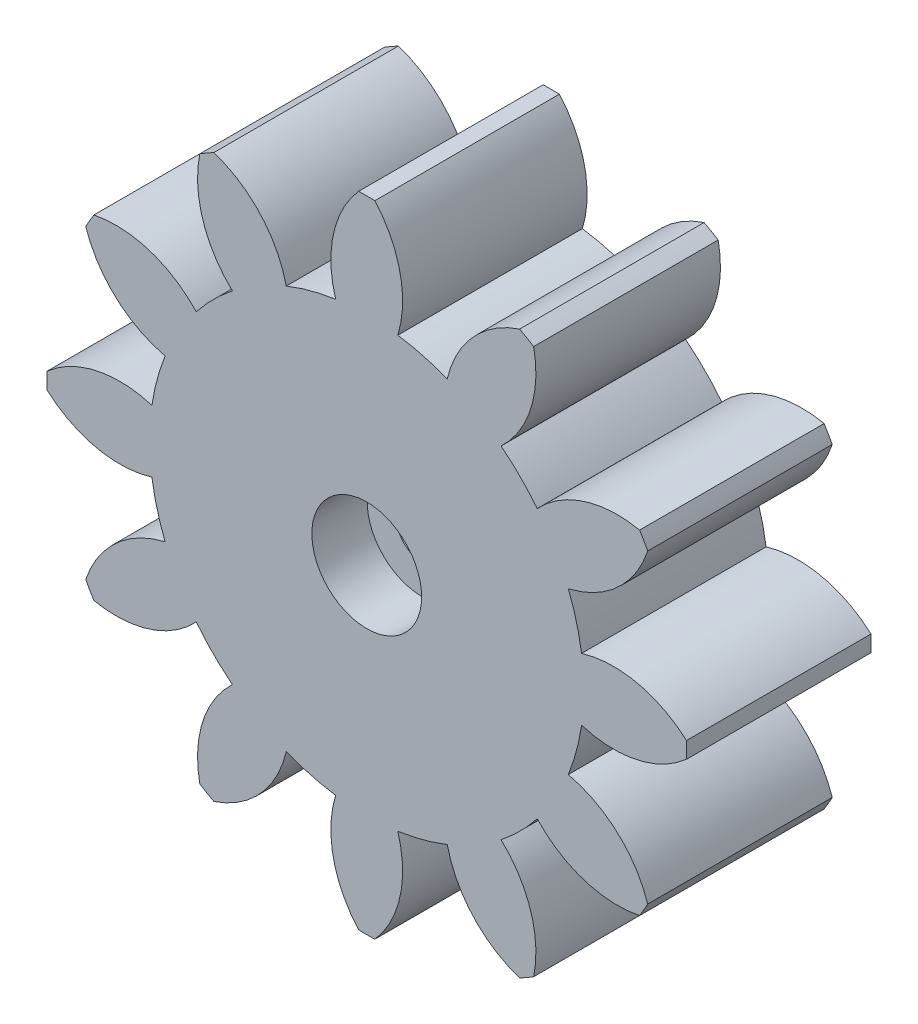
SolidWorks part; units mm, degrees
ref_plane "Front Plane" through (0, 0, 0) normal (0, 0, 1) x (1, 0, 0)
ref_plane "Top Plane" through (0, 0, 0) normal (0, 1, 0) x (1, 0, 0)
ref_plane "Right Plane" through (0, 0, 0) normal (1, 0, 0) x (0, 0, -1)
sketch "Sketch1" plane through (0, 0, 0) normal (0, 0, 1) x (1, 0, 0)
  arc A96 (10.9244, -4.3614) -> (11.6416, -1.6851) centre (0, 0) ccw
  arc A97 (11.6416, -1.6851) -> (17.3299, -0.4402) centre (13.3779, 3.9992) ccw
  arc A98 (17.3299, -0.4402) -> (17.3299, 0.4402) centre (0, 0) ccw
  arc A99 (17.3299, 0.4402) -> (11.6416, 1.6851) centre (13.3779, -3.9992) ccw
  arc A100 (11.6416, 1.6851) -> (10.9244, 4.3614) centre (0, 0) ccw
  arc A101 (10.9244, 4.3614) -> (15.2282, 8.2838) centre (9.586, 10.1524) ccw
  arc A102 (15.2282, 8.2838) -> (14.7881, 9.0462) centre (0, 0) ccw
  arc A103 (14.7881, 9.0462) -> (9.2393, 7.2801) centre (13.5852, 3.2255) ccw
  arc A104 (9.2393, 7.2801) -> (7.2801, 9.2393) centre (0, 0) ccw
  arc A105 (7.2801, 9.2393) -> (9.0462, 14.7881) centre (3.2255, 13.5852) ccw
  arc A106 (9.0462, 14.7881) -> (8.2838, 15.2282) centre (0, 0) ccw
  arc A107 (8.2838, 15.2282) -> (4.3614, 10.9244) centre (10.1524, 9.586) ccw
  arc A108 (4.3614, 10.9244) -> (1.6851, 11.6416) centre (0, 0) ccw
  arc A109 (1.6851, 11.6416) -> (0.4402, 17.3299) centre (-3.9992, 13.3779) ccw
  arc A110 (0.4402, 17.3299) -> (-0.4402, 17.3299) centre (0, 0) ccw
  arc A111 (-0.4402, 17.3299) -> (-1.6851, 11.6416) centre (3.9992, 13.3779) ccw
  arc A112 (-1.6851, 11.6416) -> (-4.3614, 10.9244) centre (0, 0) ccw
  arc A113 (-4.3614, 10.9244) -> (-8.2838, 15.2282) centre (-10.1524, 9.586) ccw
  arc A114 (-8.2838, 15.2282) -> (-9.0462, 14.7881) centre (0, 0) ccw
  arc A115 (-9.0462, 14.7881) -> (-7.2801, 9.2393) centre (-3.2255, 13.5852) ccw
  arc A116 (-7.2801, 9.2393) -> (-9.2393, 7.2801) centre (0, 0) ccw
  arc A117 (-9.2393, 7.2801) -> (-14.7881, 9.0462) centre (-13.5852, 3.2255) ccw
  arc A118 (-14.7881, 9.0462) -> (-15.2282, 8.2838) centre (0, 0) ccw
  arc A119 (-15.2282, 8.2838) -> (-10.9244, 4.3614) centre (-9.586, 10.1524) ccw
  arc A120 (-10.9244, 4.3614) -> (-11.6416, 1.6851) centre (0, 0) ccw
  arc A121 (-11.6416, 1.6851) -> (-17.3299, 0.4402) centre (-13.3779, -3.9992) ccw
  arc A122 (-17.3299, 0.4402) -> (-17.3299, -0.4402) centre (0, 0) ccw
  arc A123 (-17.3299, -0.4402) -> (-11.6416, -1.6851) centre (-13.3779, 3.9992) ccw
  arc A124 (-11.6416, -1.6851) -> (-10.9244, -4.3614) centre (0, 0) ccw
  arc A125 (-10.9244, -4.3614) -> (-15.2282, -8.2838) centre (-9.586, -10.1524) ccw
  arc A126 (-15.2282, -8.2838) -> (-14.7881, -9.0462) centre (0, 0) ccw
  arc A127 (-14.7881, -9.0462) -> (-9.2393, -7.2801) centre (-13.5852, -3.2255) ccw
  arc A128 (-9.2393, -7.2801) -> (-7.2801, -9.2393) centre (0, 0) ccw
  arc A129 (-7.2801, -9.2393) -> (-9.0462, -14.7881) centre (-3.2255, -13.5852) ccw
  arc A130 (-9.0462, -14.7881) -> (-8.2838, -15.2282) centre (0, 0) ccw
  arc A131 (-8.2838, -15.2282) -> (-4.3614, -10.9244) centre (-10.1524, -9.586) ccw
  arc A132 (-4.3614, -10.9244) -> (-1.6851, -11.6416) centre (0, 0) ccw
  arc A133 (-1.6851, -11.6416) -> (-0.4402, -17.3299) centre (3.9992, -13.3779) ccw
  arc A134 (-0.4402, -17.3299) -> (0.4402, -17.3299) centre (0, 0) ccw
  arc A135 (0.4402, -17.3299) -> (1.6851, -11.6416) centre (-3.9992, -13.3779) ccw
  arc A136 (1.6851, -11.6416) -> (4.3614, -10.9244) centre (0, 0) ccw
  arc A137 (4.3614, -10.9244) -> (8.2838, -15.2282) centre (10.1524, -9.586) ccw
  arc A138 (8.2838, -15.2282) -> (9.0462, -14.7881) centre (0, 0) ccw
  arc A139 (9.0462, -14.7881) -> (7.2801, -9.2393) centre (3.2255, -13.5852) ccw
  arc A140 (7.2801, -9.2393) -> (9.2393, -7.2801) centre (0, 0) ccw
  arc A141 (9.2393, -7.2801) -> (14.7881, -9.0462) centre (13.5852, -3.2255) ccw
  arc A142 (14.7881, -9.0462) -> (15.2282, -8.2838) centre (0, 0) ccw
  arc A143 (15.2282, -8.2838) -> (10.9244, -4.3614) centre (9.586, -10.1524) ccw
extrude "Boss-Extrude1" add sketch "Sketch1" along normal blind 10
sketch "Sketch3" plane through (0, 0, 10) normal (0, 0, 1) x (1, 0, 0)
  circle A0 centre (0, 0) radius 2.975
  dimension "D1" = 5.95
extrude "Cut-Extrude1" cut sketch "Sketch3" against normal blind 3
sketch "Sketch4" plane through (0, 0, 0) normal (0, 0, -1) x (-1, 0, 0)
  circle A0 centre (0, 0) radius 2.975 construction
  circle A1 centre (0, 0) radius 2.975
extrude "Cut-Extrude2" cut sketch "Sketch4" against normal offset from surface (5 mm away) 2 up to face at (2.975, 0, 7)
sketch "Sketch5" plane through (0, 0, 5) normal (0, 0, -1) x (-1, 0, 0)
  circle A0 centre (0, 0) radius 1.375
  dimension "D1" = 2.75
extrude "Cut-Extrude3" cut sketch "Sketch5" against normal up to next
sketch "Sketch6" plane through (0, 0, 0) normal (0, 0, -1) x (-1, 0, 0)
  text T0 "<i>Top</i>" font "Century Gothic" height in points 8
extrude "Cut-Extrude4" cut sketch "Sketch6" against normal blind 0.4
sketch "Sketch7" plane through (0, 0, 10) normal (0, 0, 1) x (1, 0, 0)
  point P0 (0, 0)
sketch "Sketch8" plane through (0, 0, 10) normal (0, 0, 1) x (1, 0, 0)
  line L0 (0, 0) -> (0, -17.3355) construction
  arc A0 (-0.4402, -17.3299) -> (0.4402, -17.3299) centre (0, 0) ccw construction
